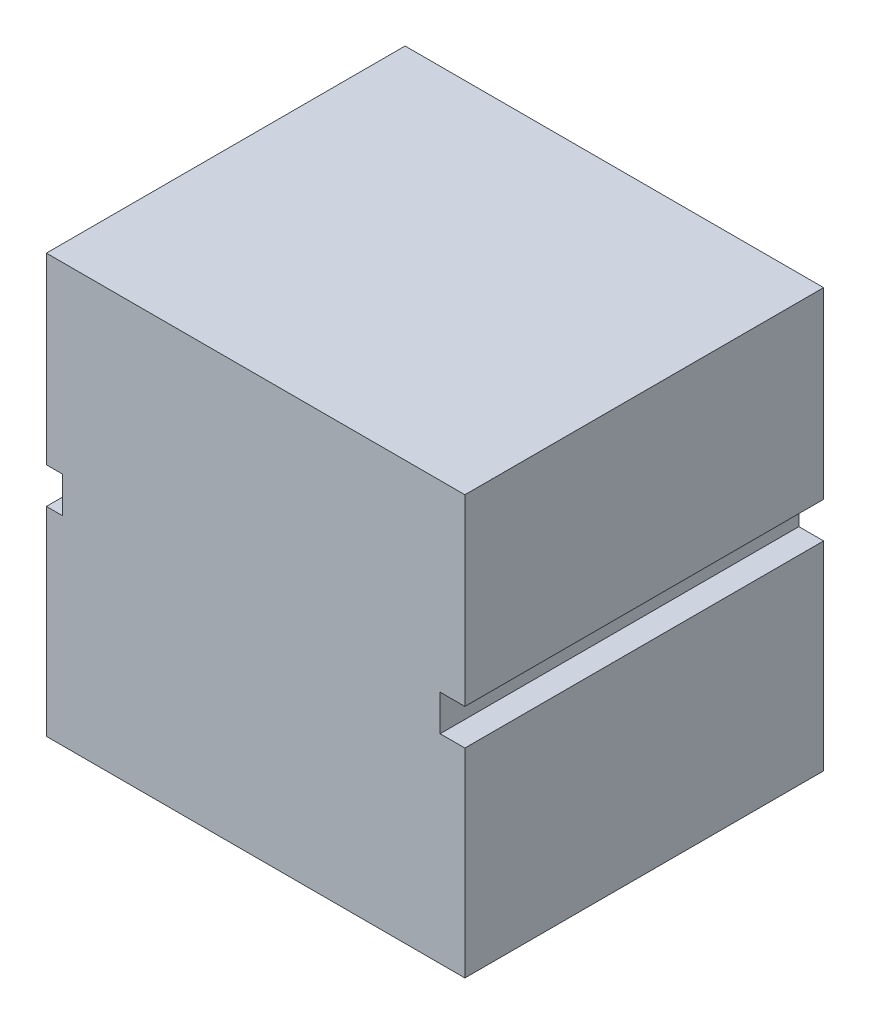
SolidWorks part; units mm, degrees
ref_plane "Plan de face" through (0, 0, 0) normal (0, 0, 1) x (1, 0, 0)
ref_plane "Plan de dessus" through (0, 0, 0) normal (0, 1, 0) x (1, 0, 0)
ref_plane "Plan de droite" through (0, 0, 0) normal (1, 0, 0) x (0, 0, -1)
sketch "Esquisse1" plane through (0, 0, 0) normal (0, 0, 1) x (1, 0, 0)
  line L1 (0, 0) -> (7, 0)
  line L2 (0, 0) -> (0, 7)
  line L3 (0, 7) -> (7, 7)
  line L4 (7, 0) -> (7, 7)
  dimension "D1" = 7
  dimension "D2" = 7
extrude "Boss.-Extru.1" add sketch "Esquisse1" along normal blind 6
sketch "Esquisse2" plane through (0, 0, 0) normal (0, 0, -1) x (-1, 0, 0)
  line L0 (-7, 0) -> (-7, 7) construction
  line L1 (-7, 3.9335) -> (-6.586, 3.9335)
  line L2 (-7, 3.9335) -> (-7, 3.331)
  line L3 (-7, 3.331) -> (-6.586, 3.331)
  line L4 (-6.586, 3.9335) -> (-6.586, 3.331)
  line L5 (0, 7) -> (0, 0) construction
  line L6 (0, 3.9335) -> (-0.267, 3.9335)
  line L7 (0, 3.9335) -> (0, 3.331)
  line L8 (0, 3.331) -> (-0.267, 3.331)
  line L9 (-0.267, 3.9335) -> (-0.267, 3.331)
extrude "Enlèv. mat.-Extru.1" cut sketch "Esquisse2" against normal through all
